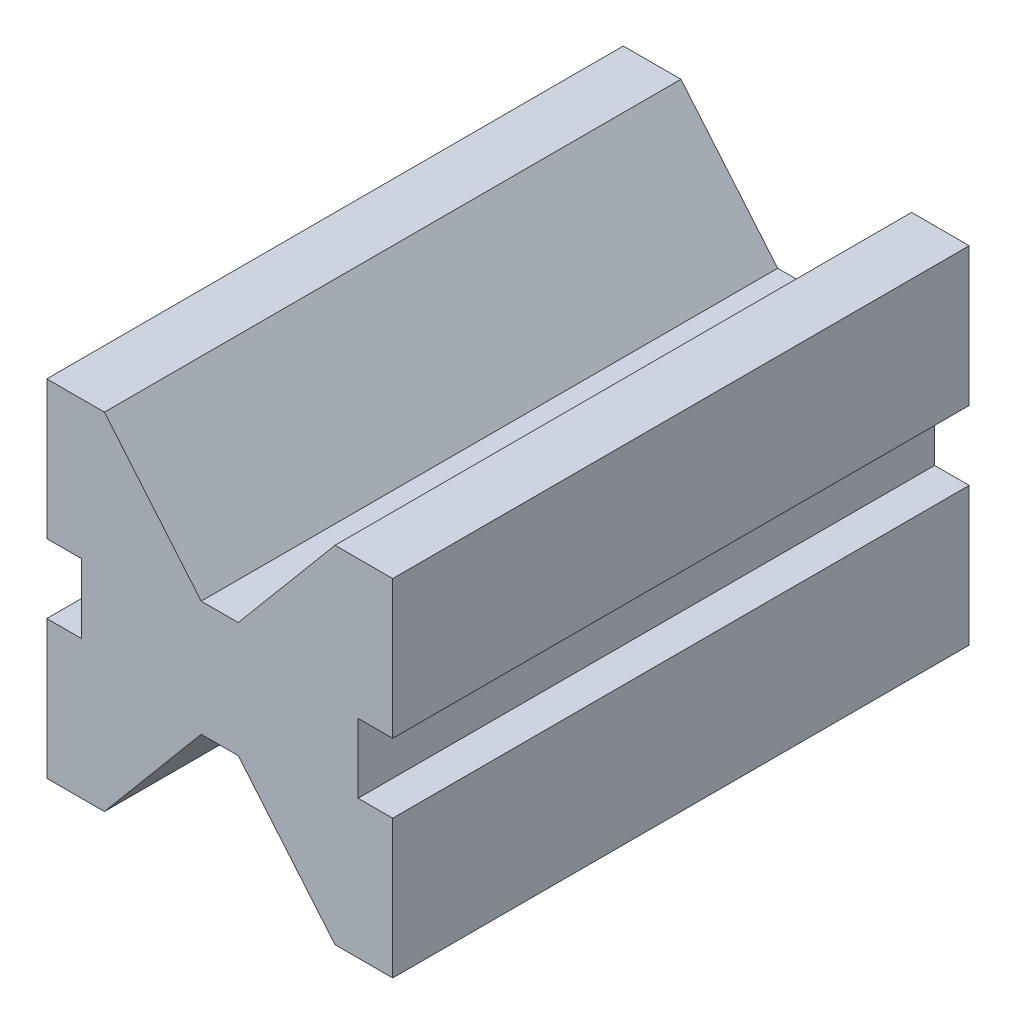
SolidWorks part; units mm, degrees
material "1060 Alloy"
ref_plane "Front Plane" through (0, 0, 0) normal (0, 0, 1) x (1, 0, 0)
ref_plane "Top Plane" through (0, 0, 0) normal (0, 1, 0) x (1, 0, 0)
ref_plane "Right Plane" through (0, 0, 0) normal (1, 0, 0) x (0, 0, -1)
sketch "Sketch1" plane through (0, 0, 0) normal (0, 0, 1) x (1, 0, 0)
  line L1 (0, 0) -> (60, 0)
  line L2 (0, 0) -> (0, 60)
  line L3 (0, 60) -> (60, 60)
  line L4 (60, 0) -> (60, 60)
  dimension "D1" = 60
  dimension "D2" = 60
extrude "Boss-Extrude1" add sketch "Sketch1" against normal blind 100
sketch "Sketch3" plane through (0, 0, 0) normal (0, 0, 1) x (1, 0, 0)
  line L0 (30, -1000) -> (30, 49000) construction
  line L1 (0, 0) -> (60, 0) construction
  line L2 (26.782, 20) -> (33.218, 20)
  line L3 (-940, 30) -> (49060, 30) construction
  line L4 (60, 0) -> (60, 60) construction
  line L5 (10, 0) -> (26.782, 20)
  line L6 (60, 60) -> (0, 60) construction
  line L7 (50, 0) -> (33.218, 20)
  line L8 (10, 0) -> (50, 0)
  line L9 (26.782, 40) -> (33.218, 40)
  line L10 (10, 60) -> (26.782, 40)
  line L11 (50, 60) -> (33.218, 40)
  line L12 (10, 60) -> (50, 60)
  line L13 (60, 24) -> (60, 36)
  line L14 (60, 36) -> (54, 36)
  line L15 (54, 36) -> (54, 24)
  line L16 (54, 24) -> (60, 24)
  line L17 (0, 24) -> (0, 36)
  line L18 (6, 24) -> (0, 24)
  line L19 (6, 36) -> (6, 24)
  line L20 (0, 36) -> (6, 36)
  point P5 (30, 0)
  point P12 (60, 30)
  dimension "D1" = 10
  dimension "D2" = 50
  dimension "D3" = 20
  dimension "D4" = 6
  dimension "D5" = 24
  dimension "D6" = 24
extrude "Cut-Extrude2" cut sketch "Sketch3" against normal through all
